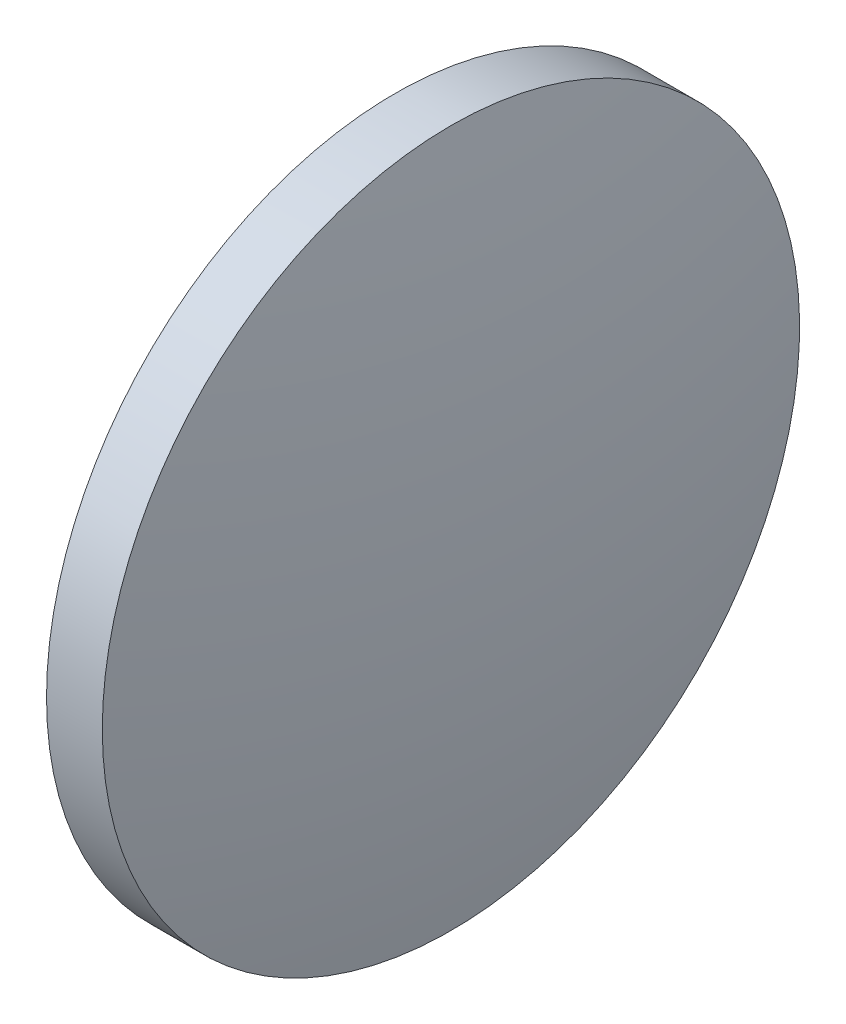
SolidWorks part; units mm, degrees
ref_plane "前视基准面" through (0, 0, 0) normal (0, 0, 1) x (1, 0, 0)
ref_plane "上视基准面" through (0, 0, 0) normal (0, 1, 0) x (1, 0, 0)
ref_plane "右视基准面" through (0, 0, 0) normal (1, 0, 0) x (0, 0, -1)
sketch "草图2" plane through (0, 0, 0) normal (0, 0, 1) x (1, 0, 0)
  line L0 (659.3288, 112.6778) -> (668.9169, 112.6778) construction
  line L1 (661.6945, 112.6778) -> (661.6945, 125.1778)
  line L2 (664.9145, 112.6778) -> (661.6945, 112.6778)
  line L5 (661.6945, 125.1778) -> (663.6945, 125.1778)
  arc A0 (664.9145, 112.6778) -> (663.6945, 125.1778) centre (600.2676, 112.6778) ccw
revolve "旋转2" add sketch "草图2" angle 360 about L0
